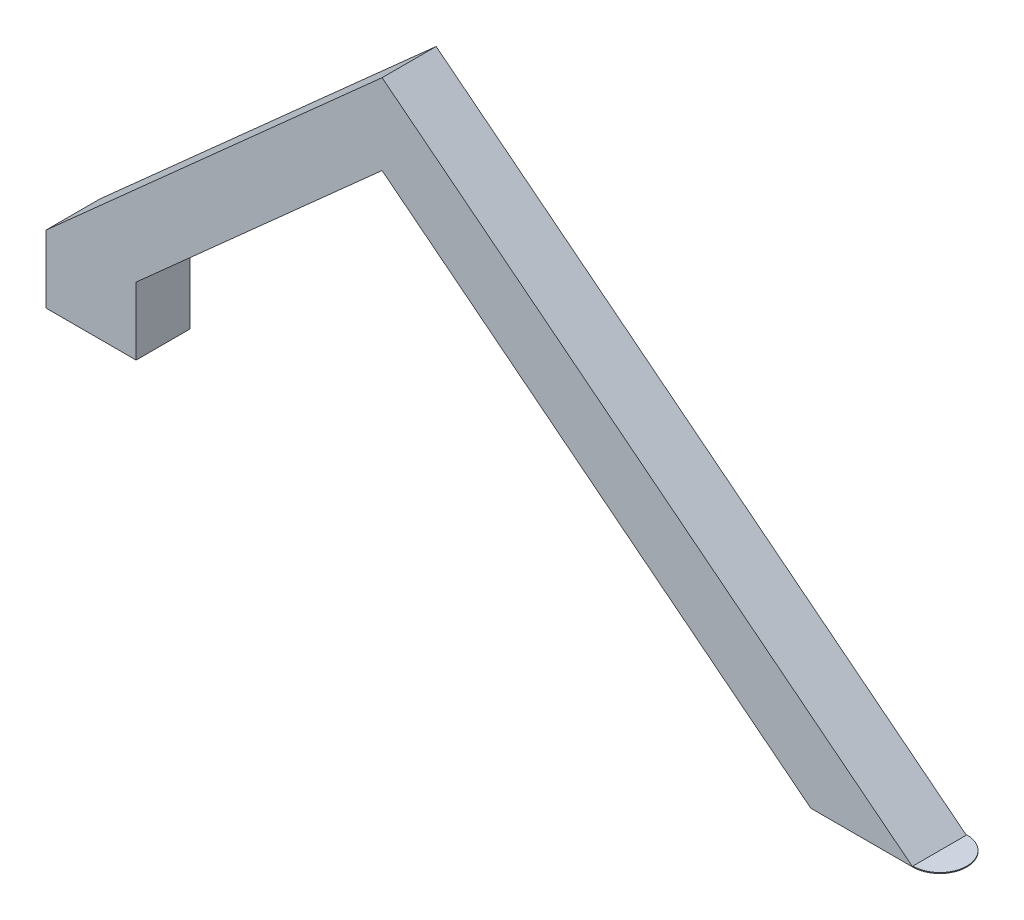
SolidWorks part; units mm, degrees
ref_plane "Front Plane" through (0, 0, 0) normal (0, 0, 1) x (1, 0, 0)
ref_plane "Top Plane" through (0, 0, 0) normal (0, 1, 0) x (1, 0, 0)
ref_plane "Right Plane" through (0, 0, 0) normal (1, 0, 0) x (0, 0, -1)
sketch "Sketch1" plane through (0, 0, 0) normal (0, 0, 1) x (1, 0, 0)
  line L0 (-10, 0) -> (-10, 15)
  line L1 (-10, 15) -> (64.6003, 81.5943)
  line L2 (64.6003, 81.5943) -> (182.4054, -11.2602)
  line L3 (10, 0) -> (10, 15)
  line L4 (10, 15) -> (64.6003, 63.7406)
  line L5 (64.6003, 63.7406) -> (159.7544, -11.2602)
  line L6 (159.7544, -11.2602) -> (182.4054, -11.2602)
  line L7 (-10, 0) -> (10, 0)
  dimension "D1" = 10
  dimension "D2" = 10
  dimension "D3" = 15
  dimension "D4" = 15
  dimension "D5" = 22.651
  dimension "D6" = 150
  dimension "D7" = 100
  dimension "D8" = 100
extrude "Boss-Extrude1" add sketch "Sketch1" along normal blind 12
sketch "Sketch3" plane through (0, -11.2602, 0) normal (0, -1, 0) x (1, 0, 0)
  line L0 (182.4054, 12) -> (182.4054, 0) construction
  line L1 (182.4054, 12) -> (182.4054, 0)
  arc A0 (182.4054, 12) -> (182.4054, 0) centre (182.4054, 6) cw
  dimension "D1" = 6
extrude "Boss-Extrude2" add sketch "Sketch3" against normal blind 0.2 separate body
sketch "Sketch4" plane through (0, 0, 0) normal (0, -1, 0) x (1, 0, 0)
  circle A0 centre (0, 6) radius 1
  dimension "D1" = 2
extrude "Cut-Extrude1" cut sketch "Sketch4" against normal blind 1
